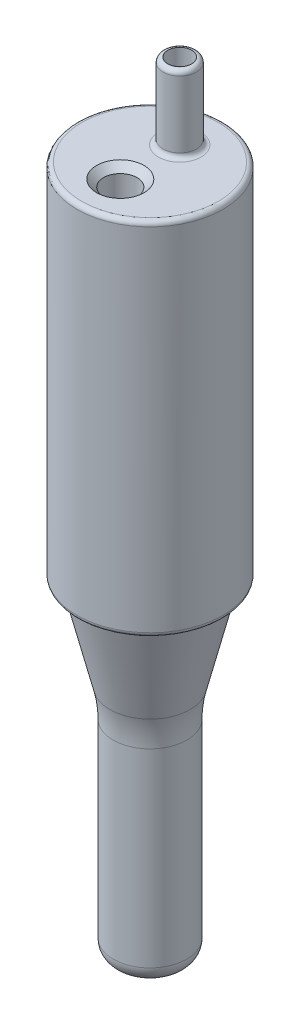
SolidWorks part; units mm, degrees
material "Резина"
ref_plane "Спереди" through (0, 0, 0) normal (0, 0, 1) x (1, 0, 0)
ref_plane "Сверху" through (0, 0, 0) normal (0, 1, 0) x (1, 0, 0)
ref_plane "Справа" through (0, 0, 0) normal (1, 0, 0) x (0, 0, -1)
sketch "Эскиз1" plane through (0, 0, 0) normal (1, 0, 0) x (0, 0, -1)
  line L0 (7.81, 0) -> (7.81, 38.61)
  line L1 (7.81, 0) -> (6.73, 0)
  line L2 (6.73, 0) -> (4.2867, -9.9945)
  line L3 (3.9351, -13) -> (3.9351, -33.2967)
  line L4 (2.9135, -34.9197) -> (2.1351, -34.9197)
  line L5 (7.81, 38.61) -> (0, 38.61)
  line L6 (2.1351, -34.9197) -> (0, -34.9197)
  line L7 (0, -34.9197) -> (0, 38.61) construction
  line L8 (0, 38.61) -> (0, -34.9197)
  arc A0 (4.2867, -9.9945) -> (3.9351, -13) centre (16.2348, -12.9154) ccw
  arc A1 (2.9135, -34.9197) -> (3.9351, -33.2967) centre (2.1351, -33.2967) ccw
  point P2 (4.2867, -9.9945)
  point P4 (3.9351, -13)
  point P7 (4.2867, -9.9945)
  point P8 (2.9135, -34.9197)
revolve "Повернуть1" add sketch "Эскиз1" angle 360 about L7
sketch "Эскиз2" plane through (0, 38.61, 0) normal (0, 1, 0) x (1, 0, 0)
  line L0 (0, -7.6501) -> (0, 8.3499) construction
  circle A0 centre (0, 0) radius 3.18
  circle A1 centre (0, -3.18) radius 1.785
  circle A2 centre (0, 3.18) radius 1.785
  circle A3 centre (0, -3.18) radius 1.27
  circle A4 centre (0, 3.18) radius 1.27
  point P13 (0, -3.18)
extrude "Бобышка-Вытянуть2" add sketch "Эскиз2" along normal blind 8.13 contours L0 A4 A0 A2 | A4 L0 A2 A0 | A2 L0 A4 A0 | L0 A2 A0 A4
fillet "Скругление1" radius 0.5 1 edges at (0, 46.74, -1.395)
ref_plane "Плоскость1" through (0, 46.74, 0) normal (0, 1, 0) x (1, 0, 0)
sketch "Эскиз4" plane through (0, 46.74, 0) normal (0, 1, 0) x (1, 0, 0)
  circle A0 centre (0, 3.18) radius 1.27
fillet "Скругление2" radius 0.5 1 edges at (0, 38.61, -1.395)
fillet "Скругление3" radius 0.5 2 edges at (0, 0, -7.81) (0, 38.61, -7.81)
sketch3d "Трехмерный эскиз1" plane through (0, 0, 0) normal (0, 0, 1) x (1, 0, 0)
ref_plane "Плоскость2" through (0, 39.61, 0) normal (0, 1, 0) x (1, 0, 0)
sketch "Эскиз5" plane through (0, 39.61, 0) normal (0, 1, 0) x (1, 0, 0)
  line L0 (0, 3.18) -> (0, -3.18) construction
  circle A0 centre (0, 0) radius 3.18
  circle A1 centre (0, -3.18) radius 1.785
extrude "Вырез-Вытянуть1" cut sketch "Эскиз5" against normal blind 18 contours A1 L0 A0 | L0 A1 A0 | A0 A1
chamfer "Фаска1" distance 0.75 angle 45 1 edges at (0, 38.61, 4.965)
